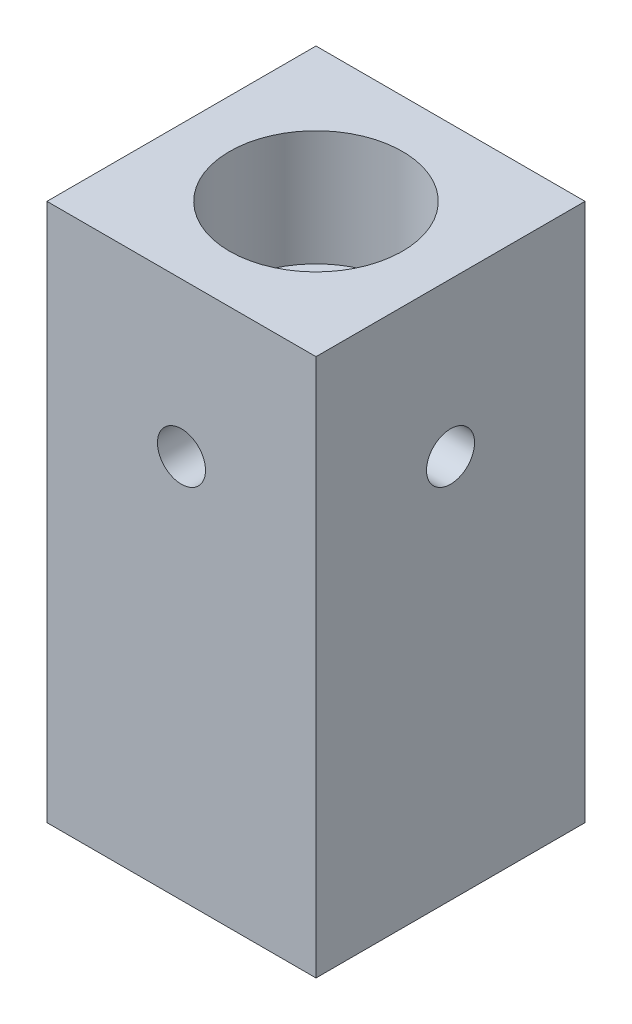
SolidWorks part; units mm, degrees
material "PE High Density"
ref_plane "Front Plane" through (0, 0, 0) normal (0, 0, 1) x (1, 0, 0)
ref_plane "Top Plane" through (0, 0, 0) normal (0, 1, 0) x (1, 0, 0)
ref_plane "Right Plane" through (0, 0, 0) normal (1, 0, 0) x (0, 0, -1)
sketch "Sketch1" plane through (0, 0, 0) normal (0, 1, 0) x (1, 0, 0)
  line L1 (11.1125, -11.1125) -> (-11.1125, -11.1125)
  line L2 (11.1125, -11.1125) -> (11.1125, 11.1125)
  line L3 (11.1125, 11.1125) -> (-11.1125, 11.1125)
  line L4 (-11.1125, -11.1125) -> (-11.1125, 11.1125)
  line L5 (11.1125, -11.1125) -> (-11.1125, 11.1125) construction
  line L6 (11.1125, 11.1125) -> (-11.1125, -11.1125) construction
  point P0 (0, 0)
  dimension "D1" = 22.225
  dimension "D2" = 22.225
extrude "Boss-Extrude1" add sketch "Sketch1" along normal blind 44.45
hole_wizard "M10x1.5 Tapped Hole1" positions "Sketch3" profile "Sketch4" tap size "M10x1.5" standard "ANSI Metric"
sketch "Sketch3" plane through (0, 0, 0) normal (0, -1, 0) x (-1, 0, 0)
  point P0 (0, 0)
cosmetic thread "Hole Thread1" parameters "D1"=20.066, "D2"=10
sketch "Sketch4" plane through (0, 0, 0) normal (1, 0, 0) x (0, 0, -1)
  line L0 (0, 0) -> (0, 27.1917)
  line L1 (0, 27.1917) -> (4.25, 24.638)
  line L2 (4.25, 24.638) -> (4.25, 0)
  line L5 (4.25, 0) -> (0, 0)
  line L10 (0, 27.1917) -> (-4.25, 24.638) construction
  line L11 (0, -6.35) -> (0, 107.95) construction
  dimension "Tap Drill Dia." = 8.5
  dimension "Tap Drill Depth" = 24.638
  dimension "Drill Angle" = 118
sketch "Sketch9" plane through (0, 44.45, 0) normal (0, 1, 0) x (1, 0, 0)
  circle A0 centre (0, 0) radius 4.25
  dimension "D1" = 8.5
extrude "Cut-Extrude1" cut sketch "Sketch9" against normal offset from surface (19.05 mm away) 25.4 up to face at (0, 0, -4.25)
sketch "Sketch10" plane through (0, 44.45, 0) normal (0, 1, 0) x (1, 0, 0)
  circle A0 centre (0, 0) radius 7.1438
  dimension "D1" = 14.2875
extrude "Cut-Extrude2" cut sketch "Sketch10" against normal blind 9.525
sketch "Sketch11" plane through (11.1125, 0, 0) normal (1, 0, 0) x (0, 0, -1)
  line L0 (0, 31.75) -> (0, 44.45) construction
  line L1 (-11.1125, 44.45) -> (11.1125, 44.45) construction
  circle A0 centre (0, 31.75) radius 1.9844
  dimension "D2" = 3.9688
  dimension "D1" = 12.7
extrude "Cut-Extrude3" cut sketch "Sketch11" against normal through all
sketch "Sketch12" plane through (0, 0, 11.1125) normal (0, 0, 1) x (1, 0, 0)
  line L0 (0, 44.45) -> (0, 31.75) construction
  line L1 (11.1125, 44.45) -> (-11.1125, 44.45) construction
  circle A0 centre (0, 31.75) radius 1.9844
  dimension "D1" = 3.9688
  dimension "D2" = 12.7
extrude "Cut-Extrude4" cut sketch "Sketch12" against normal through all
